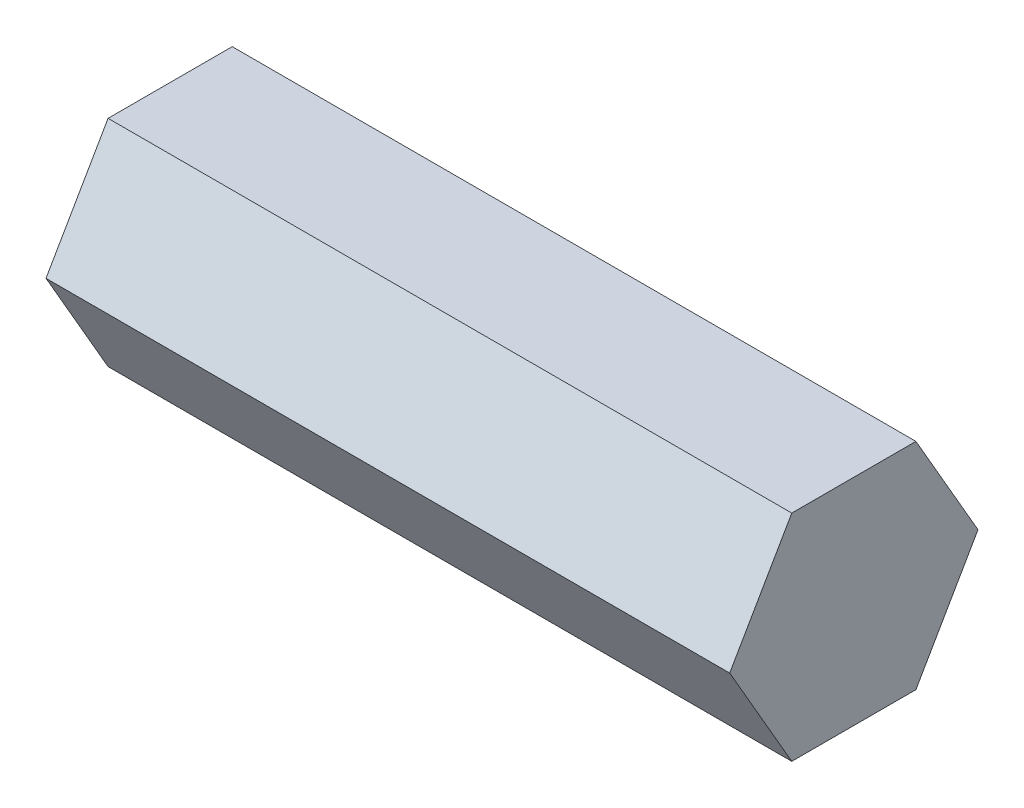
SolidWorks part; units mm, degrees
ref_plane "Front Plane" through (0, 0, 0) normal (0, 0, 1) x (1, 0, 0)
ref_plane "Top Plane" through (0, 0, 0) normal (0, 1, 0) x (1, 0, 0)
ref_plane "Right Plane" through (0, 0, 0) normal (1, 0, 0) x (0, 0, -1)
sketch "Sketch1" plane through (0, 0, 0) normal (1, 0, 0) x (0, 0, -1)
  line L1 (7.3323, 0) -> (3.6662, 6.35)
  line L2 (3.6662, 6.35) -> (-3.6662, 6.35)
  line L3 (-3.6662, 6.35) -> (-7.3323, 0)
  line L4 (-7.3323, 0) -> (-3.6662, -6.35)
  line L5 (-3.6662, -6.35) -> (3.6662, -6.35)
  line L6 (3.6662, -6.35) -> (7.3323, 0)
  circle A0 centre (0, 0) radius 6.35 construction
  dimension "D1" = 12.7
extrude "Boss-Extrude1" add sketch "Sketch1" along normal blind 40.38
